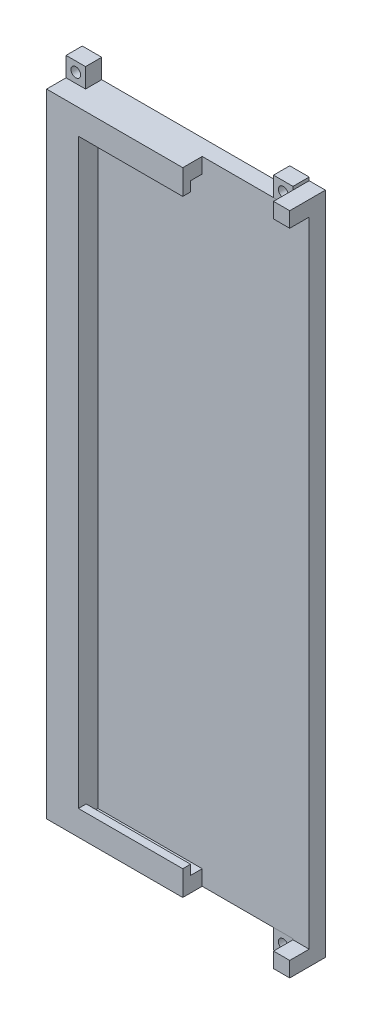
SolidWorks part; units mm, degrees
ref_plane "Front Plane" through (0, 0, 0) normal (1, 0, 0) x (0, 1, 0)
ref_plane "Top Plane" through (0, 0, 0) normal (0, 0, 1) x (0, 1, 0)
ref_plane "Right Plane" through (0, 0, 0) normal (0, 1, 0) x (-1, 0, 0)
sketch "Sketch1" plane through (0, 0, 0) normal (0, 0, 1) x (0, 1, 0)
  line L2 (-97.5, 5) -> (-97.5, 75)
  line L3 (-97.5, 75) -> (97.5, 75)
  line L4 (97.5, 5) -> (97.5, 75)
  line L5 (-102.5, 0) -> (-102.5, 5)
  line L6 (-102.5, 5) -> (-97.5, 5)
  line L7 (0, 75) -> (0, 0) construction
  line L9 (102.5, 0) -> (102.5, 5)
  line L10 (102.5, 5) -> (97.5, 5)
  line L11 (-102.5, 0) -> (102.5, 0)
  dimension "D1" = 195
  dimension "D2" = 5
  dimension "D3" = 5
  dimension "D4" = 75
extrude "Boss-Extrude1" add sketch "Sketch1" along normal blind 5
sketch "Sketch4" plane through (0, 0, 5) normal (0, 0, 1) x (1, 0, 0)
  line L0 (-75, 97.5) -> (-75, -97.5)
  line L1 (-5, 97.8) -> (0, 97.8)
  line L2 (-5, 97.8) -> (-5, 102.5)
  line L3 (-5, 102.5) -> (0, 102.5)
  line L4 (0, 97.8) -> (0, 102.5)
  line L9 (-75, 97.5) -> (-33, 97.5)
  line L11 (-65.2, 92.8) -> (-33, 92.8)
  line L12 (-33, 97.5) -> (-33, 92.8)
  line L13 (-75, -97.5) -> (-33, -97.5)
  line L15 (-65.2, -92.8) -> (-33, -92.8)
  line L16 (-33, -97.5) -> (-33, -92.8)
  line L17 (-65.2, 92.8) -> (-65.2, -92.8)
  line L18 (-5, 97.5) -> (-75, 97.5) construction
  line L19 (-5, 102.5) -> (-5, 97.5) construction
  line L20 (0, 0) -> (-65.2, 0) construction
  line L21 (-5, -102.5) -> (0, -102.5)
  line L22 (0, -97.8) -> (0, -102.5)
  line L23 (-5, -97.8) -> (0, -97.8)
  line L24 (-5, -97.8) -> (-5, -102.5)
  point P8 (-65.2, 0)
  dimension "D1" = 4.7
  dimension "D2" = 32.2
  dimension "D3" = 4.7
  dimension "D4" = 9.8
  dimension "D5" = 0.3
extrude "Boss-Extrude2" add sketch "Sketch4" along normal blind 6
sketch "Sketch5" plane through (-65.2, 0, 0) normal (1, 0, 0) x (0, 1, 0)
  line L0 (0, 11) -> (0, 5) construction
  line L1 (-92.8, 11) -> (-89.8, 11)
  line L2 (-92.8, 11) -> (-92.8, 8.6)
  line L3 (-92.8, 8.6) -> (-89.8, 8.6)
  line L4 (-89.8, 11) -> (-89.8, 8.6)
  line L5 (-92.8, 11) -> (92.8, 11) construction
  line L6 (-92.8, 5) -> (92.8, 5) construction
  line L7 (92.8, 8.6) -> (89.8, 8.6)
  line L8 (89.8, 11) -> (89.8, 8.6)
  line L9 (92.8, 11) -> (89.8, 11)
  line L10 (92.8, 11) -> (92.8, 8.6)
  dimension "D1" = 3
  dimension "D2" = 2.4
extrude "Boss-Extrude3" add sketch "Sketch5" along normal up to surface (32.2 mm away) up to face at (-33, -95.15, 8)
sketch "Sketch6" plane through (0, 0, 0) normal (0, 0, -1) x (1, 0, 0)
  line L0 (-40, 97.5) -> (-40, -97.5) construction
  line L1 (-5, 97.5) -> (-11, 97.5)
  line L2 (-5, 97.5) -> (-5, 103.5)
  line L3 (-5, 103.5) -> (-11, 103.5)
  line L4 (-11, 97.5) -> (-11, 103.5)
  line L5 (-75, 97.5) -> (-5, 97.5) construction
  line L6 (-5, -97.5) -> (-75, -97.5) construction
  line L7 (-75, 0) -> (0, 0) construction
  line L8 (-75, -97.5) -> (-75, 97.5) construction
  line L9 (-75, 103.5) -> (-69, 103.5)
  line L10 (-69, 97.5) -> (-69, 103.5)
  line L11 (-75, 97.5) -> (-69, 97.5)
  line L12 (-75, 97.5) -> (-75, 103.5)
  line L13 (-5, -103.5) -> (-11, -103.5)
  line L14 (-11, -97.5) -> (-11, -103.5)
  line L15 (-5, -97.5) -> (-11, -97.5)
  line L16 (-5, -97.5) -> (-5, -103.5)
  line L17 (-75, -97.5) -> (-75, -103.5)
  line L18 (-75, -97.5) -> (-69, -97.5)
  line L19 (-69, -97.5) -> (-69, -103.5)
  line L20 (-75, -103.5) -> (-69, -103.5)
  dimension "D1" = 6
extrude "Boss-Extrude4" add sketch "Sketch6" against normal blind 5 separate body
sketch "Sketch7" plane through (0, 0, 5) normal (0, 0, 1) x (1, 0, 0)
  line L0 (-11, -100.5) -> (-5, -100.5) construction
  line L1 (-11, -103.5) -> (-11, -97.5) construction
  line L2 (-5, -97.5) -> (-5, -103.5) construction
  line L3 (0, 0) -> (-65.2, 0) construction
  line L4 (-65.2, -92.8) -> (-65.2, 92.8) construction
  line L5 (-75, -100.5) -> (-69, -100.5) construction
  line L6 (-75, -103.5) -> (-75, -97.5) construction
  line L7 (-69, -97.5) -> (-69, -103.5) construction
  circle A0 centre (-8, -100.5) radius 1.5
  circle A1 centre (-72, -100.5) radius 1.5
  circle A2 centre (-8, 100.5) radius 1.5
  circle A3 centre (-72, 100.5) radius 1.5
  dimension "D1" = 3
  dimension "D2" = 3
extrude "Cut-Extrude1" cut sketch "Sketch7" against normal through all
